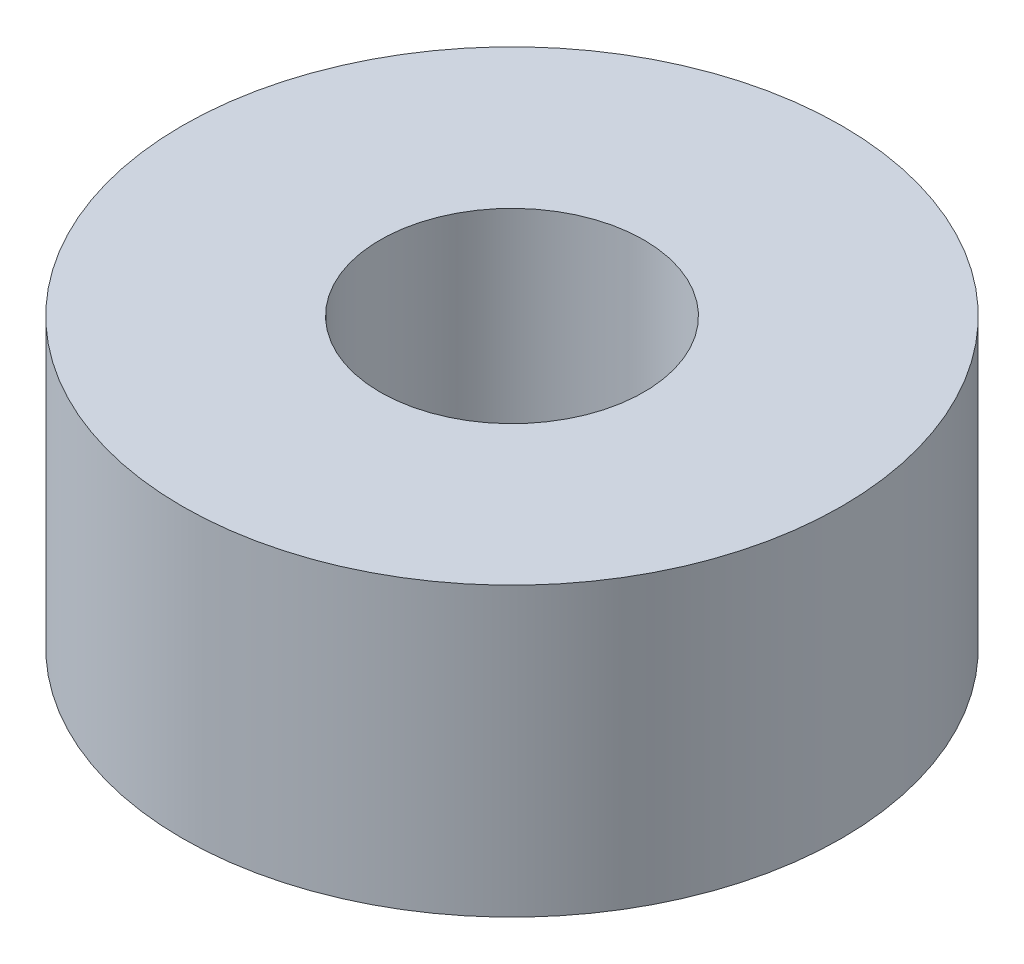
SolidWorks part; units mm, degrees
material "Nylon 101"
ref_plane "Front Plane" through (0, 0, 0) normal (0, 0, 1) x (1, 0, 0)
ref_plane "Top Plane" through (0, 0, 0) normal (0, 1, 0) x (1, 0, 0)
ref_plane "Right Plane" through (0, 0, 0) normal (1, 0, 0) x (0, 0, -1)
sketch "Sketch1" plane through (0, 0, 0) normal (0, 1, 0) x (1, 0, 0)
  circle A0 centre (0, 0) radius 2.54
  circle A1 centre (0, 0) radius 6.35
  dimension "D1" = 5.08
  dimension "D2" = 12.7
extrude "Boss-Extrude1" add sketch "Sketch1" along normal blind 5.5372
